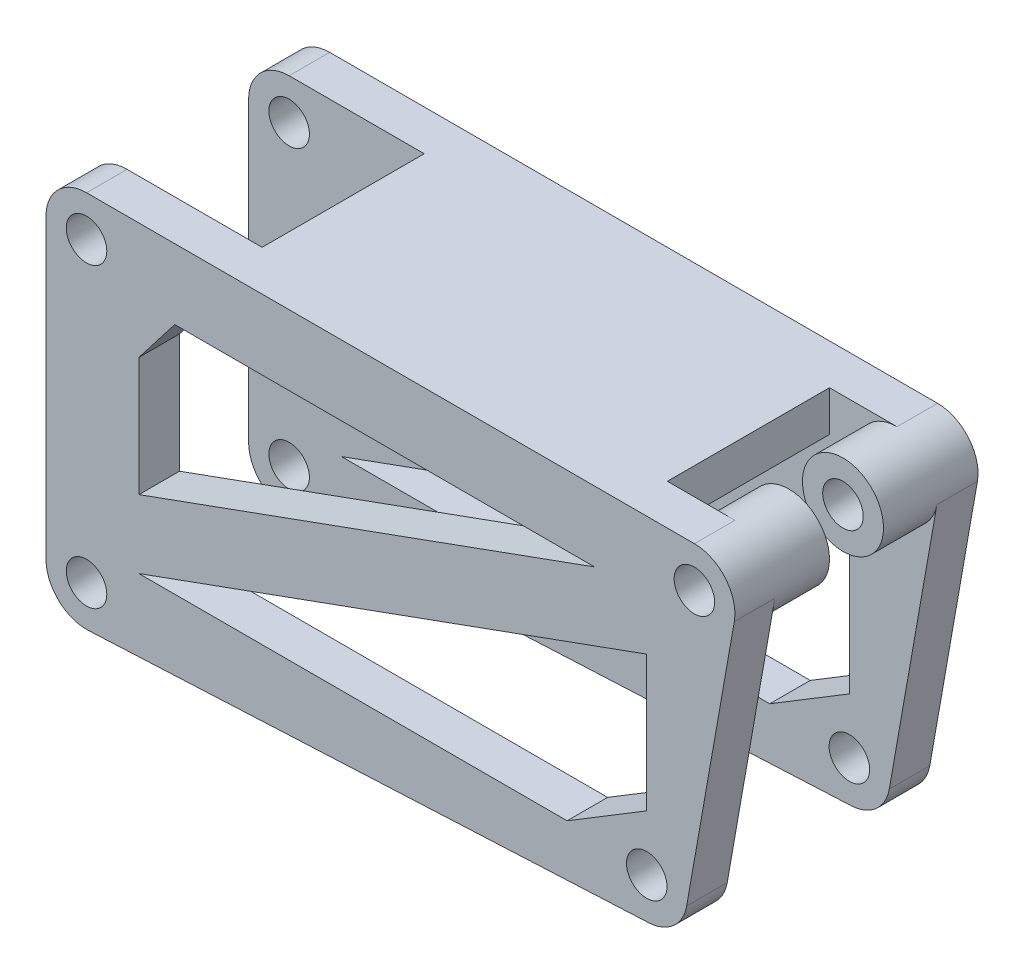
SolidWorks part; units mm, degrees
ref_plane "Front Plane" through (0, 0, 0) normal (0, 0, 1) x (1, 0, 0)
ref_plane "Top Plane" through (0, 0, 0) normal (0, 1, 0) x (1, 0, 0)
ref_plane "Right Plane" through (0, 0, 0) normal (1, 0, 0) x (0, 0, -1)
sketch "Sketch1" plane through (0, 0, 0) normal (0, 0, 1) x (1, 0, 0)
  line L0 (0, 3) -> (45, 3)
  line L1 (47.9544, -0.5209) -> (44.4279, -20.5209)
  line L2 (41.618, -22.9965) -> (0.1445, -24.9965)
  line L3 (-3, -22) -> (-3, 0)
  line L8 (3.8811, -14.414) -> (3.8811, -5.6136)
  line L9 (3.8811, -5.6136) -> (6.529, -2.1869)
  line L10 (6.529, -2.1869) -> (37.603, -2.1869)
  line L11 (37.603, -2.1869) -> (3.8811, -14.414)
  line L12 (3.8811, -19.4762) -> (41.4735, -5.8457)
  line L13 (41.4735, -5.8457) -> (41.4735, -15.8937)
  line L14 (41.4735, -15.8937) -> (35.5781, -19.4762)
  line L15 (35.5781, -19.4762) -> (3.8811, -19.4762)
  circle A0 centre (45, 0) radius 1.5
  circle A1 centre (41.4735, -20) radius 1.5
  arc A3 (45, 3) -> (47.9544, -0.5209) centre (45, 0) cw
  arc A4 (44.4279, -20.5209) -> (41.618, -22.9965) centre (41.4735, -20) cw
  arc A5 (-3, -22) -> (0.1445, -24.9965) centre (0, -22) ccw
  circle A6 centre (0, -22) radius 1.5
  arc A7 (-3, 0) -> (0, 3) centre (0, 0) cw
  circle A8 centre (0, 0) radius 1.5
  dimension "D1" = 3
  dimension "D6" = 3
  dimension "D9" = 3
  dimension "D2" = 3
  dimension "D3" = 20
  dimension "D4" = 80
  dimension "D5" = 3
  dimension "D10" = 25
  dimension "D11" = 45
extrude "Boss-Extrude1" add sketch "Sketch1" along normal blind 3
pattern_linear "LPattern1" count 2 spacing 15 along (0, 0, 1) of "Boss-Extrude1"
sketch "Sketch2" plane through (0, 0, 3) normal (0, 0, 1) x (1, 0, 0)
  circle A0 centre (45, 0) radius 3
  circle A2 centre (45, 0) radius 1.5 construction
  circle A3 centre (45, 0) radius 1.5
  dimension "D1" = 1.5
extrude "Boss-Extrude2" add sketch "Sketch2" along normal blind 4
pattern_linear "LPattern2" count 2 spacing 8 along (0, 0, 1) of "Boss-Extrude2"
sketch "Sketch3" plane through (0, 0, 3) normal (0, 0, 1) x (1, 0, 0)
  line L0 (45, 3) -> (0, 3) construction
  line L1 (40, 3) -> (10, 3)
  line L2 (40, 3) -> (40, 0)
  line L3 (40, 0) -> (10, 0)
  line L4 (10, 3) -> (10, 0)
  dimension "D1" = 3
  dimension "D2" = 30
  dimension "D3" = 5
extrude "Boss-Extrude3" add sketch "Sketch3" along normal up to next (15 mm away)
